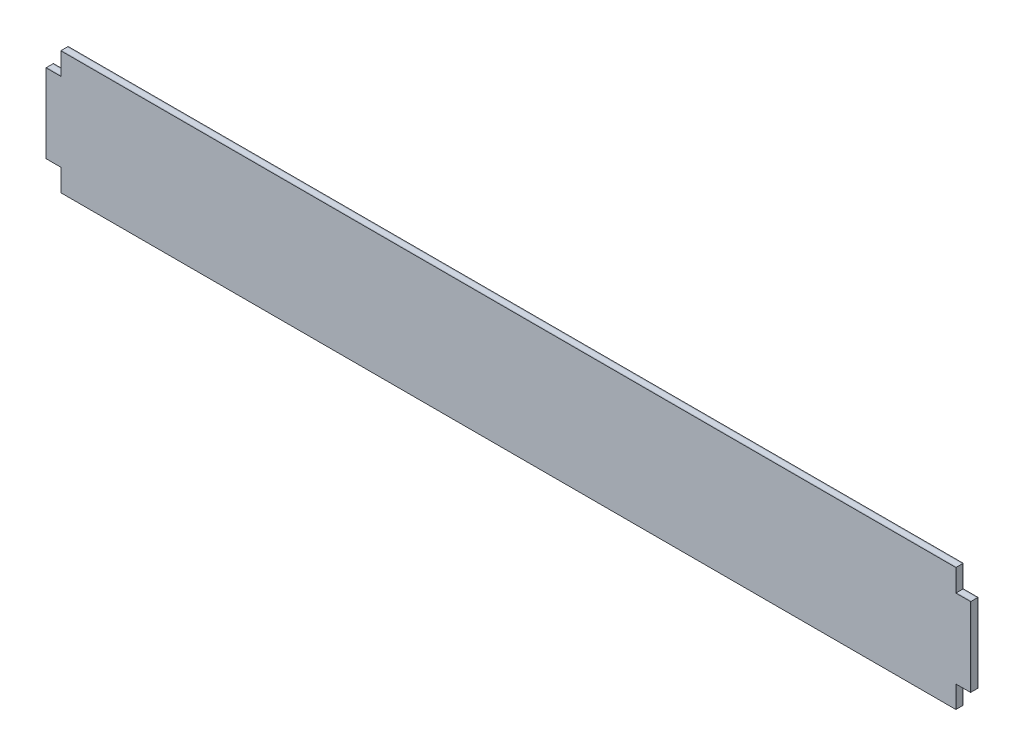
SolidWorks part; units mm, degrees
ref_plane "Front Plane" through (0, 0, 0) normal (0, 0, 1) x (1, 0, 0)
ref_plane "Top Plane" through (0, 0, 0) normal (0, 1, 0) x (1, 0, 0)
ref_plane "Right Plane" through (0, 0, 0) normal (1, 0, 0) x (0, 0, -1)
sketch "Sketch1" plane through (0, 0, 0) normal (0, 0, 1) x (1, 0, 0)
  line L0 (-182, 25) -> (-182, 16)
  line L1 (-182, 25) -> (182, 25)
  line L2 (-188, 16) -> (-188, -16)
  line L3 (-182, -25) -> (182, -25)
  line L4 (188, 16) -> (188, -16)
  line L5 (-182, 16) -> (-188, 16)
  line L6 (-193.8387, 0) -> (-175.5618, 0) construction
  line L7 (0, 8.6095) -> (0, -10.0827) construction
  line L8 (-182, -16) -> (-188, -16)
  line L9 (-182, -25) -> (-182, -16)
  line L10 (182, -25) -> (182, -16)
  line L11 (182, -16) -> (188, -16)
  line L12 (182, 16) -> (188, 16)
  line L13 (182, 25) -> (182, 16)
  point P0 (0, 0)
  dimension "D3" = 9
  dimension "D4" = 6
extrude "Boss-Extrude1" add sketch "Sketch1" along normal blind 0.25
sketch "Sketch2" plane through (0, 0, 0) normal (0, 0, -1) x (-1, 0, 0)
  line L12 (182, 25) -> (-182, 25)
  line L13 (-182, 25) -> (-182, 16)
  line L14 (-182, 16) -> (-188, 16)
  line L15 (-188, 16) -> (-188, -16)
  line L16 (-188, -16) -> (-182, -16)
  line L17 (-182, -16) -> (-182, -25)
  line L18 (-182, -25) -> (182, -25)
  line L19 (182, -25) -> (182, -16)
  line L20 (182, -16) -> (188, -16)
  line L21 (188, -16) -> (188, 16)
  line L22 (188, 16) -> (182, 16)
  line L23 (182, 16) -> (182, 25)
  line L24 (182, 25) -> (-182, 25)
  line L25 (-182, 25) -> (-182, 16)
  line L26 (-182, 16) -> (-188, 16)
  line L27 (-188, 16) -> (-188, -16)
  line L28 (-188, -16) -> (-182, -16)
  line L29 (-182, -16) -> (-182, -25)
  line L30 (-182, -25) -> (182, -25)
  line L31 (182, -25) -> (182, -16)
  line L32 (182, -16) -> (188, -16)
  line L33 (188, -16) -> (188, 16)
  line L34 (188, 16) -> (182, 16)
  line L35 (182, 16) -> (182, 25)
  line M13 (182, 25) -> (-182, 25)
  line M14 (-182, 25) -> (-182, 16)
  line M15 (-182, 16) -> (-188, 16)
  line M16 (-188, 16) -> (-188, -16)
  line M17 (-188, -16) -> (-182, -16)
  line M18 (-182, -16) -> (-182, -25)
  line M19 (-182, -25) -> (182, -25)
  line M20 (182, -25) -> (182, -16)
  line M21 (182, -16) -> (188, -16)
  line M22 (188, -16) -> (188, 16)
  line M23 (188, 16) -> (182, 16)
  line M24 (182, 16) -> (182, 25)
  dimension "D1" = 0
extrude "Boss-Extrude2" add sketch "Sketch2" along normal blind 2.5 separate body contours M24 M13 M14 M15 M16 M17 M18 M19 M20 M21 M22 M23
sketch "Sketch3" plane through (0, 0, -2.5) normal (0, 0, -1) x (-1, 0, 0)
  line L12 (182, 16) -> (182, 25)
  line L13 (182, 25) -> (-182, 25)
  line L14 (-182, 25) -> (-182, 16)
  line L15 (-182, 16) -> (-188, 16)
  line L16 (-188, 16) -> (-188, -16)
  line L17 (-188, -16) -> (-182, -16)
  line L18 (-182, -16) -> (-182, -25)
  line L19 (-182, -25) -> (182, -25)
  line L20 (182, -25) -> (182, -16)
  line L21 (182, -16) -> (188, -16)
  line L22 (188, -16) -> (188, 16)
  line L23 (188, 16) -> (182, 16)
  line L24 (182, 16) -> (182, 25)
  line L25 (182, 25) -> (-182, 25)
  line L26 (-182, 25) -> (-182, 16)
  line L27 (-182, 16) -> (-188, 16)
  line L28 (-188, 16) -> (-188, -16)
  line L29 (-188, -16) -> (-182, -16)
  line L30 (-182, -16) -> (-182, -25)
  line L31 (-182, -25) -> (182, -25)
  line L32 (182, -25) -> (182, -16)
  line L33 (182, -16) -> (188, -16)
  line L34 (188, -16) -> (188, 16)
  line L35 (188, 16) -> (182, 16)
  dimension "D1" = 0
extrude "Boss-Extrude3" add sketch "Sketch3" along normal blind 0.25 separate body
